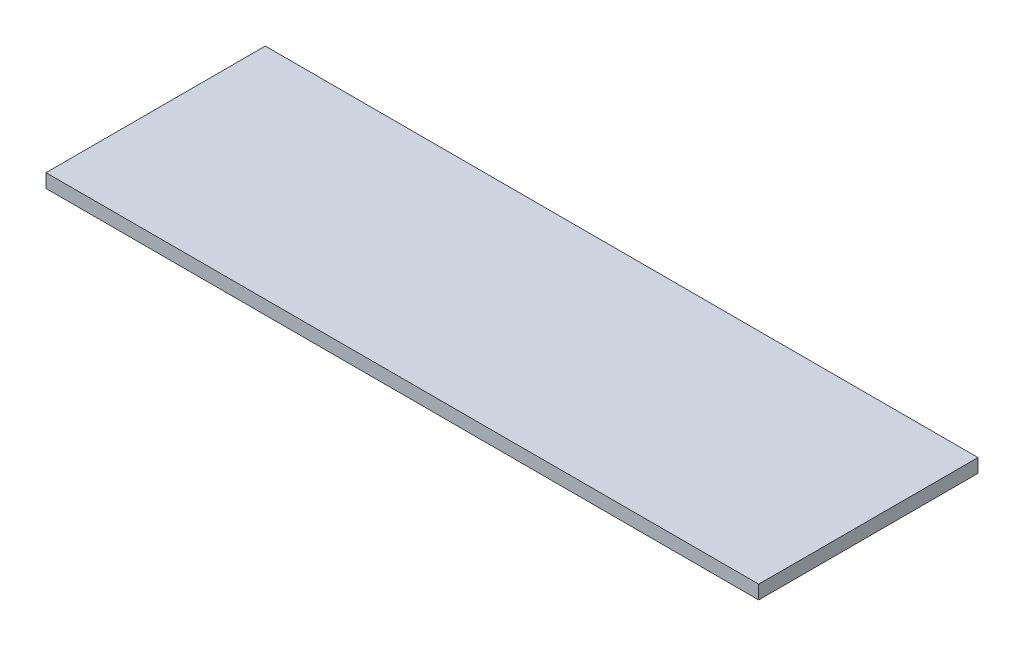
SolidWorks part; units mm, degrees
ref_plane "Front Plane" through (0, 0, 0) normal (0, 0, 1) x (1, 0, 0)
ref_plane "Top Plane" through (0, 0, 0) normal (0, 1, 0) x (1, 0, 0)
ref_plane "Right Plane" through (0, 0, 0) normal (1, 0, 0) x (0, 0, -1)
sketch "Sketch1" plane through (0, 0, 0) normal (0, 1, 0) x (1, 0, 0)
  line L1 (165.1, -50.8) -> (-165.1, -50.8)
  line L2 (165.1, -50.8) -> (165.1, 50.8)
  line L3 (165.1, 50.8) -> (-165.1, 50.8)
  line L4 (-165.1, -50.8) -> (-165.1, 50.8)
  line L5 (165.1, -50.8) -> (-165.1, 50.8) construction
  line L6 (165.1, 50.8) -> (-165.1, -50.8) construction
  point P0 (0, 0)
  dimension "D1" = 101.6
  dimension "D2" = 330.2
extrude "Boss-Extrude1" add sketch "Sketch1" along normal blind 6.35
